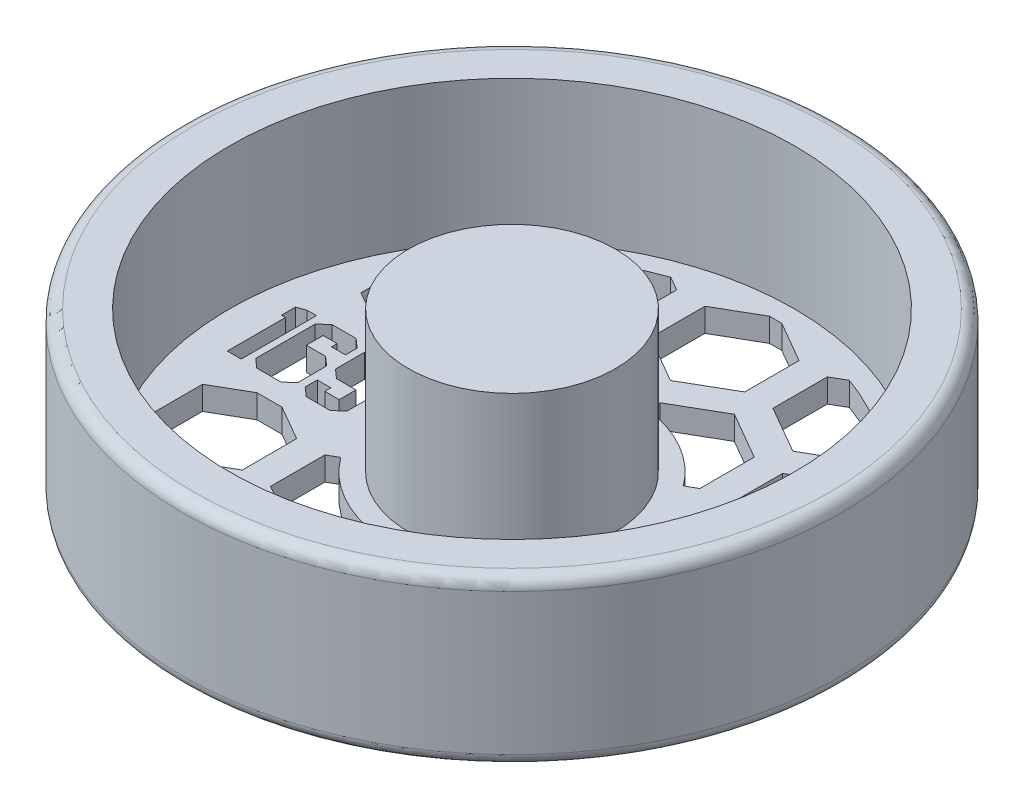
SolidWorks part; units mm, degrees
ref_plane "Front Plane" through (0, 0, 0) normal (0, 0, 1) x (1, 0, 0)
ref_plane "Top Plane" through (0, 0, 0) normal (0, 1, 0) x (1, 0, 0)
ref_plane "Right Plane" through (0, 0, 0) normal (1, 0, 0) x (0, 0, -1)
sketch "Sketch1" plane through (0, 0, 0) normal (0, 0, 1) x (1, 0, 0)
  line L0 (0, 0) -> (0, 22.225)
  line L1 (0, 22.225) -> (13.97, 22.225)
  line L2 (13.97, 22.225) -> (13.97, 3.175)
  line L3 (13.97, 3.175) -> (38.1, 3.175)
  line L4 (38.1, 3.175) -> (38.1, 22.225)
  line L5 (38.1, 22.225) -> (42.8625, 22.225)
  line L6 (44.45, 20.6375) -> (44.45, 1.5875)
  line L7 (42.8625, 0) -> (0, 0)
  arc A0 (42.8625, 0) -> (44.45, 1.5875) centre (42.8625, 1.5875) ccw
  arc A1 (44.45, 20.6375) -> (42.8625, 22.225) centre (42.8625, 20.6375) ccw
  dimension "D7" = 1.5875
  dimension "D1" = 3.175
  dimension "D2" = 6.35
  dimension "D3" = 38.1
  dimension "D4" = 13.97
  dimension "D5" = 19.05
  dimension "D6" = 19.05
revolve "Revolve1" add sketch "Sketch1" angle 360 about L0
sketch "Sketch2" plane through (0, 3.175, 0) normal (0, 1, 0) x (1, 0, 0)
  line L0 (-13.97, 0) -> (-38.1, 0) construction
  line L1 (13.97, 0) -> (38.1, 0) construction
  line L2 (-13.97, -5.08) -> (-38.1, -5.08) construction
  line L3 (13.97, -3.81) -> (38.1, -3.81) construction
  circle A0 centre (0, 0) radius 13.97 construction
  circle A1 centre (0, 0) radius 13.97 construction
  circle A2 centre (0, 0) radius 38.1 construction
  circle A3 centre (0, 0) radius 38.1 construction
  text T0 "169" font "Jersey M54" height 10.16
  text T1 "3/4" font "Century Gothic" height 7.62
  dimension "D1" = 5.08
  dimension "D2" = 3.81
extrude "Cut-Extrude1" cut sketch "Sketch2" against normal through all both and the other way through all
sketch "Sketch3" plane through (0, 3.175, 0) normal (0, 1, 0) x (1, 0, 0)
  line L0 (0, -7.9375) -> (0, 7.9375)
  line L1 (-34.6628, 7.9375) -> (34.6628, 7.9375)
  line L2 (-34.6628, -7.9375) -> (34.6628, -7.9375)
  line L3 (16.51, -7.3323) -> (22.86, -3.6662)
  line L4 (0, -7.3323) -> (6.35, -3.6662)
  line L5 (6.35, -3.6662) -> (6.35, 3.6662)
  line L6 (6.35, 3.6662) -> (0, 7.3323)
  line L7 (0, 7.3323) -> (-6.35, 3.6662)
  line L8 (-6.35, 3.6662) -> (-6.35, -3.6662)
  line L9 (-6.35, -3.6662) -> (0, -7.3323)
  line L10 (8.255, -6.9657) -> (1.905, -10.6319)
  line L11 (1.905, -10.6319) -> (1.905, -17.9643)
  line L12 (1.905, -17.9643) -> (8.255, -21.6304)
  line L13 (8.255, -21.6304) -> (14.605, -17.9643)
  line L14 (14.605, -17.9643) -> (14.605, -10.6319)
  line L15 (14.605, -10.6319) -> (8.255, -6.9657)
  line L16 (22.86, -3.6662) -> (22.86, 3.6662)
  line L17 (22.86, 3.6662) -> (16.51, 7.3323)
  line L18 (16.51, 7.3323) -> (10.16, 3.6662)
  line L19 (10.16, 3.6662) -> (10.16, -3.6662)
  line L20 (10.16, -3.6662) -> (16.51, -7.3323)
  line L21 (24.765, -6.9657) -> (18.415, -10.6319)
  line L22 (18.415, -10.6319) -> (18.415, -17.9643)
  line L23 (18.415, -17.9643) -> (24.765, -21.6304)
  line L24 (24.765, -21.6304) -> (31.115, -17.9643)
  line L25 (31.115, -17.9643) -> (31.115, -10.6319)
  line L26 (31.115, -10.6319) -> (24.765, -6.9657)
  line L27 (33.02, -7.3323) -> (39.37, -3.6662)
  line L28 (39.37, -3.6662) -> (39.37, 3.6662)
  line L29 (39.37, 3.6662) -> (33.02, 7.3323)
  line L30 (33.02, 7.3323) -> (26.67, 3.6662)
  line L31 (26.67, 3.6662) -> (26.67, -3.6662)
  line L32 (26.67, -3.6662) -> (33.02, -7.3323)
  line L33 (41.275, -6.9657) -> (34.925, -10.6319)
  line L34 (34.925, -10.6319) -> (34.925, -17.9643)
  line L35 (34.925, -17.9643) -> (41.275, -21.6304)
  line L36 (41.275, -21.6304) -> (47.625, -17.9643)
  line L37 (47.625, -17.9643) -> (47.625, -10.6319)
  line L38 (47.625, -10.6319) -> (41.275, -6.9657)
  line L39 (-16.51, -7.3323) -> (-10.16, -3.6662)
  line L40 (-10.16, -3.6662) -> (-10.16, 3.6662)
  line L41 (-10.16, 3.6662) -> (-16.51, 7.3323)
  line L42 (-16.51, 7.3323) -> (-22.86, 3.6662)
  line L43 (-22.86, 3.6662) -> (-22.86, -3.6662)
  line L44 (-22.86, -3.6662) -> (-16.51, -7.3323)
  line L45 (-8.255, -6.9657) -> (-14.605, -10.6319)
  line L46 (-14.605, -10.6319) -> (-14.605, -17.9643)
  line L47 (-14.605, -17.9643) -> (-8.255, -21.6304)
  line L48 (-8.255, -21.6304) -> (-1.905, -17.9643)
  line L49 (-1.905, -17.9643) -> (-1.905, -10.6319)
  line L50 (-1.905, -10.6319) -> (-8.255, -6.9657)
  line L51 (-33.02, -7.3323) -> (-26.67, -3.6662)
  line L52 (-26.67, -3.6662) -> (-26.67, 3.6662)
  line L53 (-26.67, 3.6662) -> (-33.02, 7.3323)
  line L54 (-33.02, 7.3323) -> (-39.37, 3.6662)
  line L55 (-39.37, 3.6662) -> (-39.37, -3.6662)
  line L56 (-39.37, -3.6662) -> (-33.02, -7.3323)
  line L57 (-24.765, -6.9657) -> (-31.115, -10.6319)
  line L58 (-31.115, -10.6319) -> (-31.115, -17.9643)
  line L59 (-31.115, -17.9643) -> (-24.765, -21.6304)
  line L60 (-24.765, -21.6304) -> (-18.415, -17.9643)
  line L61 (-18.415, -17.9643) -> (-18.415, -10.6319)
  line L62 (-18.415, -10.6319) -> (-24.765, -6.9657)
  line L63 (-49.53, -7.3323) -> (-43.18, -3.6662)
  line L64 (-43.18, -3.6662) -> (-43.18, 3.6662)
  line L65 (-43.18, 3.6662) -> (-49.53, 7.3323)
  line L66 (-49.53, 7.3323) -> (-55.88, 3.6662)
  line L67 (-55.88, 3.6662) -> (-55.88, -3.6662)
  line L68 (-55.88, -3.6662) -> (-49.53, -7.3323)
  line L69 (-41.275, -6.9657) -> (-47.625, -10.6319)
  line L70 (-47.625, -10.6319) -> (-47.625, -17.9643)
  line L71 (-47.625, -17.9643) -> (-41.275, -21.6304)
  line L72 (-41.275, -21.6304) -> (-34.925, -17.9643)
  line L73 (-34.925, -17.9643) -> (-34.925, -10.6319)
  line L74 (-34.925, -10.6319) -> (-41.275, -6.9657)
  line L75 (0, 21.3697) -> (6.35, 25.0358)
  line L76 (6.35, 25.0358) -> (6.35, 32.3682)
  line L77 (6.35, 32.3682) -> (0, 36.0343)
  line L78 (0, 36.0343) -> (-6.35, 32.3682)
  line L79 (-6.35, 32.3682) -> (-6.35, 25.0358)
  line L80 (-6.35, 25.0358) -> (0, 21.3697)
  line L81 (8.255, 21.7363) -> (1.905, 18.0701)
  line L82 (1.905, 18.0701) -> (1.905, 10.7377)
  line L83 (1.905, 10.7377) -> (8.255, 7.0716)
  line L84 (8.255, 7.0716) -> (14.605, 10.7377)
  line L85 (14.605, 10.7377) -> (14.605, 18.0701)
  line L86 (14.605, 18.0701) -> (8.255, 21.7363)
  line L87 (16.51, 21.3697) -> (22.86, 25.0358)
  line L88 (22.86, 25.0358) -> (22.86, 32.3682)
  line L89 (22.86, 32.3682) -> (16.51, 36.0343)
  line L90 (16.51, 36.0343) -> (10.16, 32.3682)
  line L91 (10.16, 32.3682) -> (10.16, 25.0358)
  line L92 (10.16, 25.0358) -> (16.51, 21.3697)
  line L93 (24.765, 21.7363) -> (18.415, 18.0701)
  line L94 (18.415, 18.0701) -> (18.415, 10.7377)
  line L95 (18.415, 10.7377) -> (24.765, 7.0716)
  line L96 (24.765, 7.0716) -> (31.115, 10.7377)
  line L97 (31.115, 10.7377) -> (31.115, 18.0701)
  line L98 (31.115, 18.0701) -> (24.765, 21.7363)
  line L99 (33.02, 21.3697) -> (39.37, 25.0358)
  line L100 (39.37, 25.0358) -> (39.37, 32.3682)
  line L101 (39.37, 32.3682) -> (33.02, 36.0343)
  line L102 (33.02, 36.0343) -> (26.67, 32.3682)
  line L103 (26.67, 32.3682) -> (26.67, 25.0358)
  line L104 (26.67, 25.0358) -> (33.02, 21.3697)
  line L105 (41.275, 21.7363) -> (34.925, 18.0701)
  line L106 (34.925, 18.0701) -> (34.925, 10.7377)
  line L107 (34.925, 10.7377) -> (41.275, 7.0716)
  line L108 (41.275, 7.0716) -> (47.625, 10.7377)
  line L109 (47.625, 10.7377) -> (47.625, 18.0701)
  line L110 (47.625, 18.0701) -> (41.275, 21.7363)
  line L111 (-16.51, 21.3697) -> (-10.16, 25.0358)
  line L112 (-10.16, 25.0358) -> (-10.16, 32.3682)
  line L113 (-10.16, 32.3682) -> (-16.51, 36.0343)
  line L114 (-16.51, 36.0343) -> (-22.86, 32.3682)
  line L115 (-22.86, 32.3682) -> (-22.86, 25.0358)
  line L116 (-22.86, 25.0358) -> (-16.51, 21.3697)
  line L117 (-8.255, 21.7363) -> (-14.605, 18.0701)
  line L118 (-14.605, 18.0701) -> (-14.605, 10.7377)
  line L119 (-14.605, 10.7377) -> (-8.255, 7.0716)
  line L120 (-8.255, 7.0716) -> (-1.905, 10.7377)
  line L121 (-1.905, 10.7377) -> (-1.905, 18.0701)
  line L122 (-1.905, 18.0701) -> (-8.255, 21.7363)
  line L123 (-24.765, 21.7363) -> (-31.115, 18.0701)
  line L124 (-31.115, 18.0701) -> (-31.115, 10.7377)
  line L125 (-31.115, 10.7377) -> (-24.765, 7.0716)
  line L126 (-24.765, 7.0716) -> (-18.415, 10.7377)
  line L127 (-18.415, 10.7377) -> (-18.415, 18.0701)
  line L128 (-18.415, 18.0701) -> (-24.765, 21.7363)
  line L129 (-33.02, 21.3697) -> (-26.67, 25.0358)
  line L130 (-26.67, 25.0358) -> (-26.67, 32.3682)
  line L131 (-26.67, 32.3682) -> (-33.02, 36.0343)
  line L132 (-33.02, 36.0343) -> (-39.37, 32.3682)
  line L133 (-39.37, 32.3682) -> (-39.37, 25.0358)
  line L134 (-39.37, 25.0358) -> (-33.02, 21.3697)
  line L135 (-49.53, 21.3697) -> (-43.18, 25.0358)
  line L136 (-43.18, 25.0358) -> (-43.18, 32.3682)
  line L137 (-43.18, 32.3682) -> (-49.53, 36.0343)
  line L138 (-49.53, 36.0343) -> (-55.88, 32.3682)
  line L139 (-55.88, 32.3682) -> (-55.88, 25.0358)
  line L140 (-55.88, 25.0358) -> (-49.53, 21.3697)
  line L141 (-41.275, 21.7363) -> (-47.625, 18.0701)
  line L142 (-47.625, 18.0701) -> (-47.625, 10.7377)
  line L143 (-47.625, 10.7377) -> (-41.275, 7.0716)
  line L144 (-41.275, 7.0716) -> (-34.925, 10.7377)
  line L145 (-34.925, 10.7377) -> (-34.925, 18.0701)
  line L146 (-34.925, 18.0701) -> (-41.275, 21.7363)
  line L147 (0, -36.0343) -> (6.35, -32.3682)
  line L148 (6.35, -32.3682) -> (6.35, -25.0358)
  line L149 (6.35, -25.0358) -> (0, -21.3697)
  line L150 (0, -21.3697) -> (-6.35, -25.0358)
  line L151 (-6.35, -25.0358) -> (-6.35, -32.3682)
  line L152 (-6.35, -32.3682) -> (0, -36.0343)
  line L153 (8.255, -35.6677) -> (1.905, -39.3339)
  line L154 (1.905, -39.3339) -> (1.905, -46.6663)
  line L155 (1.905, -46.6663) -> (8.255, -50.3324)
  line L156 (8.255, -50.3324) -> (14.605, -46.6663)
  line L157 (14.605, -46.6663) -> (14.605, -39.3339)
  line L158 (14.605, -39.3339) -> (8.255, -35.6677)
  line L159 (16.51, -36.0343) -> (22.86, -32.3682)
  line L160 (22.86, -32.3682) -> (22.86, -25.0358)
  line L161 (22.86, -25.0358) -> (16.51, -21.3697)
  line L162 (16.51, -21.3697) -> (10.16, -25.0358)
  line L163 (10.16, -25.0358) -> (10.16, -32.3682)
  line L164 (10.16, -32.3682) -> (16.51, -36.0343)
  line L165 (24.765, -35.6677) -> (18.415, -39.3339)
  line L166 (18.415, -39.3339) -> (18.415, -46.6663)
  line L167 (18.415, -46.6663) -> (24.765, -50.3324)
  line L168 (24.765, -50.3324) -> (31.115, -46.6663)
  line L169 (31.115, -46.6663) -> (31.115, -39.3339)
  line L170 (31.115, -39.3339) -> (24.765, -35.6677)
  line L171 (33.02, -36.0343) -> (39.37, -32.3682)
  line L172 (39.37, -32.3682) -> (39.37, -25.0358)
  line L173 (39.37, -25.0358) -> (33.02, -21.3697)
  line L174 (33.02, -21.3697) -> (26.67, -25.0358)
  line L175 (26.67, -25.0358) -> (26.67, -32.3682)
  line L176 (26.67, -32.3682) -> (33.02, -36.0343)
  line L177 (41.275, -35.6677) -> (34.925, -39.3339)
  line L178 (34.925, -39.3339) -> (34.925, -46.6663)
  line L179 (34.925, -46.6663) -> (41.275, -50.3324)
  line L180 (41.275, -50.3324) -> (47.625, -46.6663)
  line L181 (47.625, -46.6663) -> (47.625, -39.3339)
  line L182 (47.625, -39.3339) -> (41.275, -35.6677)
  line L183 (-16.51, -36.0343) -> (-10.16, -32.3682)
  line L184 (-10.16, -32.3682) -> (-10.16, -25.0358)
  line L185 (-10.16, -25.0358) -> (-16.51, -21.3697)
  line L186 (-16.51, -21.3697) -> (-22.86, -25.0358)
  line L187 (-22.86, -25.0358) -> (-22.86, -32.3682)
  line L188 (-22.86, -32.3682) -> (-16.51, -36.0343)
  line L189 (-8.255, -35.6677) -> (-14.605, -39.3339)
  line L190 (-14.605, -39.3339) -> (-14.605, -46.6663)
  line L191 (-14.605, -46.6663) -> (-8.255, -50.3324)
  line L192 (-8.255, -50.3324) -> (-1.905, -46.6663)
  line L193 (-1.905, -46.6663) -> (-1.905, -39.3339)
  line L194 (-1.905, -39.3339) -> (-8.255, -35.6677)
  line L195 (-24.765, -35.6677) -> (-31.115, -39.3339)
  line L196 (-31.115, -39.3339) -> (-31.115, -46.6663)
  line L197 (-31.115, -46.6663) -> (-24.765, -50.3324)
  line L198 (-24.765, -50.3324) -> (-18.415, -46.6663)
  line L199 (-18.415, -46.6663) -> (-18.415, -39.3339)
  line L200 (-18.415, -39.3339) -> (-24.765, -35.6677)
  line L201 (-33.02, -36.0343) -> (-26.67, -32.3682)
  line L202 (-26.67, -32.3682) -> (-26.67, -25.0358)
  line L203 (-26.67, -25.0358) -> (-33.02, -21.3697)
  line L204 (-33.02, -21.3697) -> (-39.37, -25.0358)
  line L205 (-39.37, -25.0358) -> (-39.37, -32.3682)
  line L206 (-39.37, -32.3682) -> (-33.02, -36.0343)
  line L207 (-49.53, -36.0343) -> (-43.18, -32.3682)
  line L208 (-43.18, -32.3682) -> (-43.18, -25.0358)
  line L209 (-43.18, -25.0358) -> (-49.53, -21.3697)
  line L210 (-49.53, -21.3697) -> (-55.88, -25.0358)
  line L211 (-55.88, -25.0358) -> (-55.88, -32.3682)
  line L212 (-55.88, -32.3682) -> (-49.53, -36.0343)
  line L213 (-41.275, -35.6677) -> (-47.625, -39.3339)
  line L214 (-47.625, -39.3339) -> (-47.625, -46.6663)
  line L215 (-47.625, -46.6663) -> (-41.275, -50.3324)
  line L216 (-41.275, -50.3324) -> (-34.925, -46.6663)
  line L217 (-34.925, -46.6663) -> (-34.925, -39.3339)
  line L218 (-34.925, -39.3339) -> (-41.275, -35.6677)
  circle A0 centre (0, 0) radius 35.56
  circle A1 centre (0, 0) radius 16.51
  circle A2 centre (0, 0) radius 6.35 construction
  circle A3 centre (8.255, -14.2981) radius 6.35 construction
  point P7 (0, 0)
  point P10 (0, 7.9375)
  point P13 (0, -7.9375)
  dimension "D1" = 71.12
  dimension "D2" = 33.02
  dimension "D3" = 15.875
  dimension "D4" = 12.7
  dimension "D5" = 12.7
  dimension "D6" = 3.81
  dimension "D7" = 1.905
  dimension "D8" = 3
  dimension "D9" = 4
  dimension "D10" = 2
  dimension "D11" = 2
extrude "Cut-Extrude4" cut sketch "Sketch3" against normal through all both and the other way through all contours L113 A0 L115 L116 L111 L112 | L123 A0 L124 L125 L1 L126 L127 L128 | A1 L121 L122 L117 L118 L119 | L77 A0 L78 L79 L80 L75 L76 | L88 A0 L90 L91 L92 L87 | A1 L84 L85 L86 L81 L82 | L97 A0 L98 L93 L94 L95 L1 L96 | L24 A0 L25 L26 L2 L21 L22 L23 | A1 L11 L12 L13 L14 L15 | L164 A0 L160 L161 L162 L163 | L152 A0 L147 L148 L149 L150 L151 | A1 L45 L46 L47 L48 L49 | L187 A0 L183 L184 L185 L186 | L58 A0 L59 L60 L61 L62 L2 L57
